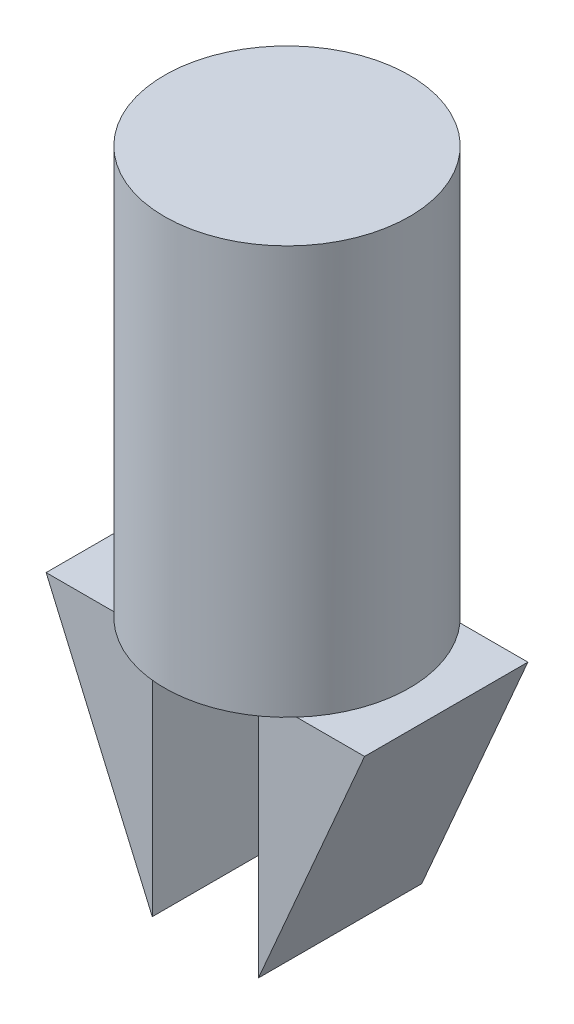
SolidWorks part; units mm, degrees
ref_plane "前视基准面" through (0, 0, 0) normal (0, 0, 1) x (1, 0, 0)
ref_plane "上视基准面" through (0, 0, 0) normal (0, 1, 0) x (1, 0, 0)
ref_plane "右视基准面" through (0, 0, 0) normal (1, 0, 0) x (0, 0, -1)
sketch "草图1" plane through (0, 0, 0) normal (0, 1, 0) x (1, 0, 0)
  circle A0 centre (0, 0) radius 15
  dimension "D1" = 30
extrude "凸台-拉伸1" add sketch "草图1" along normal blind 50
sketch "草图2" plane through (0, 0, 0) normal (0, -1, 0) x (1, 0, 0)
  line L0 (0, 0) -> (-46.2578, 0) construction
  circle A0 centre (0, 0) radius 15 construction
  circle A1 centre (0, 0) radius 15
  point P4 (-15, 0)
  point P7 (15, 0)
sketch "草图6" plane through (0, 0, 0) normal (0, 0, 1) x (1, 0, 0)
  line L0 (6.5, 0) -> (19.5, 0)
  line L1 (200000, 0) -> (-200046.2578, 0) construction
  line L2 (19.5, 0) -> (6.5, -30)
  line L3 (6.5, -30) -> (6.5, 0)
  line L4 (0, 0) -> (0, -7.7542) construction
  line L5 (-19.5, 0) -> (-6.5, -30)
  line L6 (-6.5, 0) -> (-19.5, 0)
  line L7 (-6.5, -30) -> (-6.5, 0)
  dimension "D1" = 30
  dimension "D2" = 13
  dimension "D3" = 6.5
  dimension "D4" = 6.5
extrude "凸台-拉伸5" add sketch "草图6" along normal mid plane 20 contours L5 L7 L6 | L3 L0 L2
